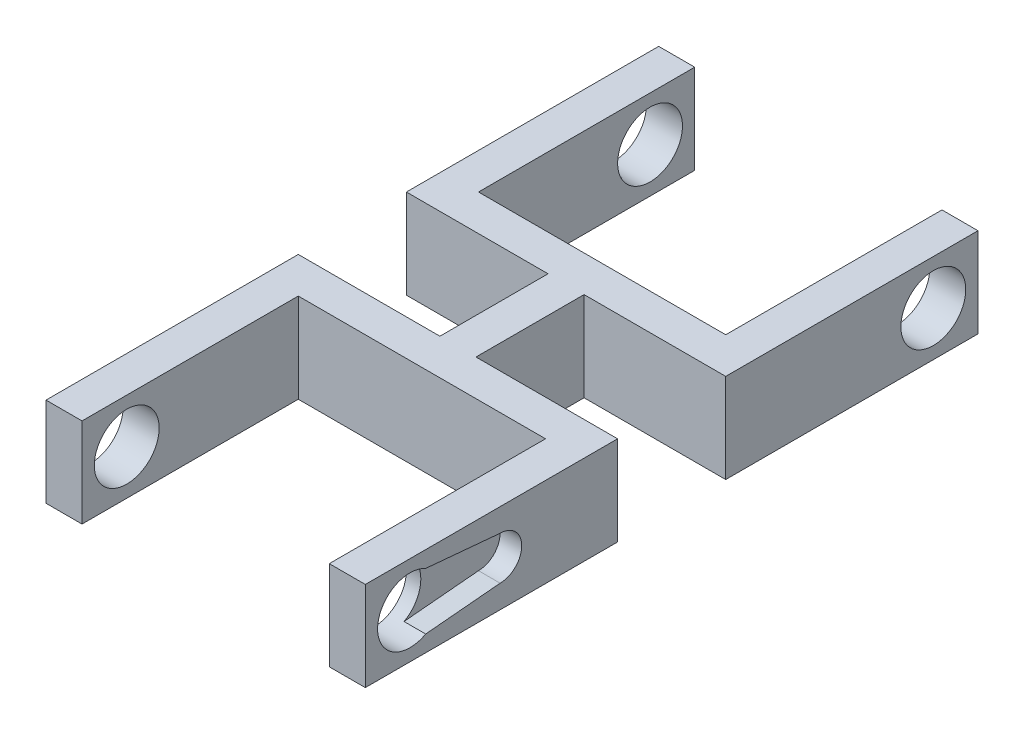
SolidWorks part; units mm, degrees
ref_plane "Front Plane" through (0, 0, 0) normal (0, 0, 1) x (1, 0, 0)
ref_plane "Top Plane" through (0, 0, 0) normal (0, 1, 0) x (1, 0, 0)
ref_plane "Right Plane" through (0, 0, 0) normal (1, 0, 0) x (0, 0, -1)
sketch "Sketch1" plane through (0, 0, 0) normal (0, 0, 1) x (1, 0, 0)
  line L1 (-22.15, 6.2) -> (22.15, 6.2)
  line L2 (-22.15, 6.2) -> (-22.15, -6.2)
  line L3 (-22.15, -6.2) -> (22.15, -6.2)
  line L4 (22.15, 6.2) -> (22.15, -6.2)
  line L5 (-22.15, 6.2) -> (22.15, -6.2) construction
  line L6 (-22.15, -6.2) -> (22.15, 6.2) construction
  point P0 (0, 0)
  dimension "D1" = 12.4
  dimension "D2" = 44.3
extrude "Boss-Extrude2" add sketch "Sketch1" along normal blind 5
sketch "Sketch2" plane through (0, 0, 5) normal (0, 0, 1) x (1, 0, 0)
  line L0 (-22.15, -6.2) -> (22.15, -6.2) construction
  line L1 (22.15, 6.2) -> (17.15, 6.2)
  line L2 (22.15, 6.2) -> (22.15, -6.2)
  line L3 (22.15, -6.2) -> (17.15, -6.2)
  line L4 (17.15, 6.2) -> (17.15, -6.2)
  line L6 (-22.15, 6.2) -> (-17.15, 6.2)
  line L7 (-22.15, 6.2) -> (-22.15, -6.2)
  line L8 (-22.15, -6.2) -> (-17.15, -6.2)
  line L9 (-17.15, 6.2) -> (-17.15, -6.2)
  dimension "D1" = 5
  dimension "D2" = 5
extrude "Boss-Extrude3" add sketch "Sketch2" along normal blind 30
sketch "Sketch3" plane through (22.15, 0, 0) normal (1, 0, 0) x (0, 0, -1)
  line L0 (-35, 6.2) -> (-35, -6.2) construction
  line L1 (-35, 0) -> (-28.8, 0) construction
  circle A0 centre (-28.8, 0) radius 4.5
  dimension "D1" = 6.2
extrude "Cut-Extrude1" cut sketch "Sketch3" against normal blind 50
sketch "Sketch5" plane through (0, 0, 0) normal (0, 0, -1) x (-1, 0, 0)
  line L0 (-22.15, 6.2) -> (22.15, 6.2) construction
  line L1 (-6.2, -6.2) -> (6.2, -6.2)
  line L2 (-6.2, -6.2) -> (-6.2, 6.2)
  line L3 (-6.2, 6.2) -> (6.2, 6.2)
  line L4 (6.2, -6.2) -> (6.2, 6.2)
  line L5 (-6.2, -6.2) -> (6.2, 6.2) construction
  line L6 (-6.2, 6.2) -> (6.2, -6.2) construction
  point P0 (0, 0)
  dimension "D1" = 12.4
extrude "Boss-Extrude5" add sketch "Sketch5" along normal blind 7.5
mirror "Mirror7" about plane through (0, 0, -7.5) normal (0, 0, 1) of "Boss-Extrude5", "Boss-Extrude3", "Boss-Extrude2", "Cut-Extrude1"
sketch "Sketch7" plane through (0, 0, -15) normal (0, 0, -1) x (-1, 0, 0)
  line L1 (-22.15, -6.2) -> (22.15, -6.2)
  line L2 (-22.15, -6.2) -> (-22.15, 6.2)
  line L3 (-22.15, 6.2) -> (22.15, 6.2)
  line L4 (22.15, -6.2) -> (22.15, 6.2)
  line L5 (-22.15, -6.2) -> (22.15, 6.2) construction
  line L6 (-22.15, 6.2) -> (22.15, -6.2) construction
  point P0 (0, 0)
  dimension "D1" = 44.3
  dimension "D2" = 12.4
extrude "Boss-Extrude6" add sketch "Sketch7" along normal blind 5
sketch "Sketch10" plane through (0, 0, -20) normal (0, 0, -1) x (-1, 0, 0)
  line L0 (-22.15, -6.2) -> (22.15, -6.2) construction
  line L1 (-22.15, 6.2) -> (-17.15, 6.2)
  line L2 (-22.15, 6.2) -> (-22.15, -6.2)
  line L3 (-22.15, -6.2) -> (-17.15, -6.2)
  line L4 (-17.15, 6.2) -> (-17.15, -6.2)
  line L6 (22.15, 6.2) -> (17.15, 6.2)
  line L7 (22.15, 6.2) -> (22.15, -6.2)
  line L8 (22.15, -6.2) -> (17.15, -6.2)
  line L9 (17.15, 6.2) -> (17.15, -6.2)
  dimension "D1" = 5
  dimension "D2" = 5
extrude "Boss-Extrude7" add sketch "Sketch10" along normal blind 30
sketch "Sketch11" plane through (-22.15, 0, 0) normal (-1, 0, 0) x (0, 0, 1)
  line L0 (-50, 0) -> (-43.8, 0) construction
  line L1 (-50, -6.2) -> (-50, 6.2) construction
  circle A0 centre (-43.8, 0) radius 4.5
  dimension "D1" = 6.2
extrude "Cut-Extrude2" cut sketch "Sketch11" against normal blind 50
sketch "Sketch12" plane through (0, 6.2, 0) normal (0, 1, 0) x (1, 0, 0)
  line L0 (0, 0) -> (-2.5, 0) construction
  line L3 (2.5, 15) -> (6.2, 15)
  line L5 (2.5, 15) -> (2.5, 0)
  line L6 (2.5, 0) -> (6.2, 0)
  line L7 (6.2, 15) -> (6.2, 0)
  line L8 (-6.2, 15) -> (-2.5, 15)
  line L9 (-6.2, 15) -> (-6.2, 0)
  line L10 (-6.2, 0) -> (-2.5, 0)
  line L11 (-2.5, 15) -> (-2.5, 0)
  dimension "D1" = 2.5
extrude "Cut-Extrude4" cut sketch "Sketch12" against normal through all
sketch "Sketch13" plane through (-22.15, 0, 0) normal (-1, 0, 0) x (0, 0, 1)
  line L2 (-31.3, 3) -> (-42.0165, 4.1315)
  line L4 (-42.0165, -4.1315) -> (-31.3, -3)
  line L5 (-31.3, 0) -> (-28.3, 0) construction
  circle A0 centre (-43.8, 0) radius 4.5 construction
  arc A1 (-31.3, -3) -> (-31.3, 3) centre (-31.3, 0) ccw
  arc A2 (-42.0165, 4.1315) -> (-42.0165, -4.1315) centre (-43.8, 0) cw
extrude "Cut-Extrude5" cut sketch "Sketch13" against normal blind 3
sketch "Sketch14" plane through (22.15, 0, 0) normal (1, 0, 0) x (0, 0, -1)
  line L0 (-33.3, 0) -> (-16.3, 0) construction
  line L1 (-16.3, 3) -> (-26.6273, 3.9407)
  line L3 (-26.6273, -3.9407) -> (-16.3, -3)
  circle A0 centre (-28.8, 0) radius 4.5 construction
  arc A1 (-16.3, -3) -> (-16.3, 3) centre (-16.3, 0) ccw
  arc A2 (-26.6273, 3.9407) -> (-26.6273, -3.9407) centre (-28.8, 0) cw
  dimension "D1" = 17
extrude "Cut-Extrude6" cut sketch "Sketch14" against normal blind 3
